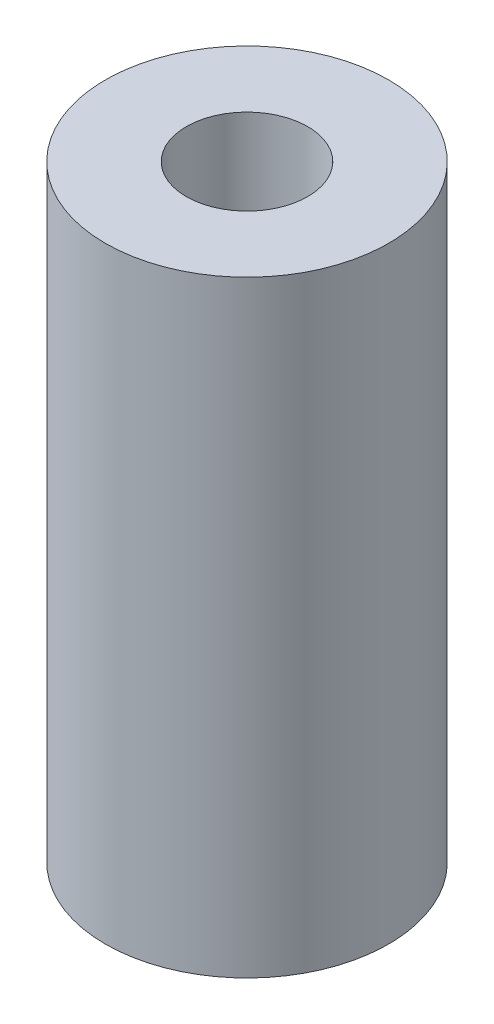
SolidWorks part; units mm, degrees
material "尼龙 101"
ref_plane "前视基准面" through (0, 0, 0) normal (0, 0, 1) x (1, 0, 0)
ref_plane "上视基准面" through (0, 0, 0) normal (0, 1, 0) x (1, 0, 0)
ref_plane "右视基准面" through (0, 0, 0) normal (1, 0, 0) x (0, 0, -1)
sketch "草图1" plane through (0, 0, 0) normal (0, 1, 0) x (1, 0, 0)
  circle A0 centre (0, 0) radius 3.5
  circle A1 centre (0, 0) radius 1.5
  dimension "D1" = 3
  dimension "D2" = 7
extrude "凸台-拉伸1" add sketch "草图1" along normal blind 15
